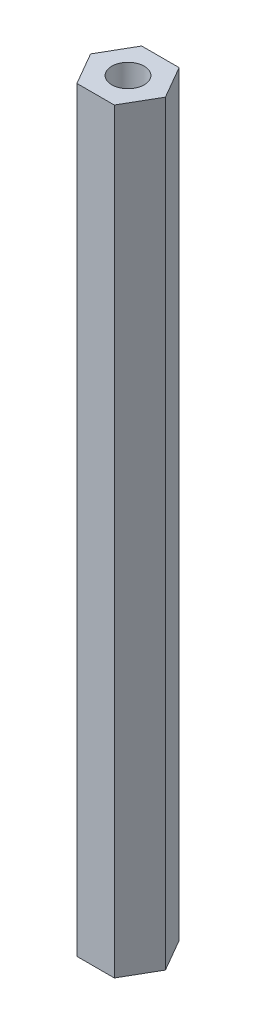
SolidWorks part; units mm, degrees
material "铜"
ref_plane "前视基准面" through (0, 0, 0) normal (0, 0, 1) x (1, 0, 0)
ref_plane "上视基准面" through (0, 0, 0) normal (0, 1, 0) x (1, 0, 0)
ref_plane "右视基准面" through (0, 0, 0) normal (1, 0, 0) x (0, 0, -1)
sketch "草图1" plane through (0, 0, 0) normal (0, 1, 0) x (1, 0, 0)
  line L1 (3.4641, 0) -> (1.7321, 3)
  line L2 (1.7321, 3) -> (-1.7321, 3)
  line L3 (-1.7321, 3) -> (-3.4641, 0)
  line L4 (-3.4641, 0) -> (-1.7321, -3)
  line L5 (-1.7321, -3) -> (1.7321, -3)
  line L6 (1.7321, -3) -> (3.4641, 0)
  circle A0 centre (0, 0) radius 1.5
  circle A1 centre (0, 0) radius 3 construction
  dimension "D1" = 3
  dimension "D2" = 6
extrude "凸台-拉伸1" add sketch "草图1" along normal blind 70
